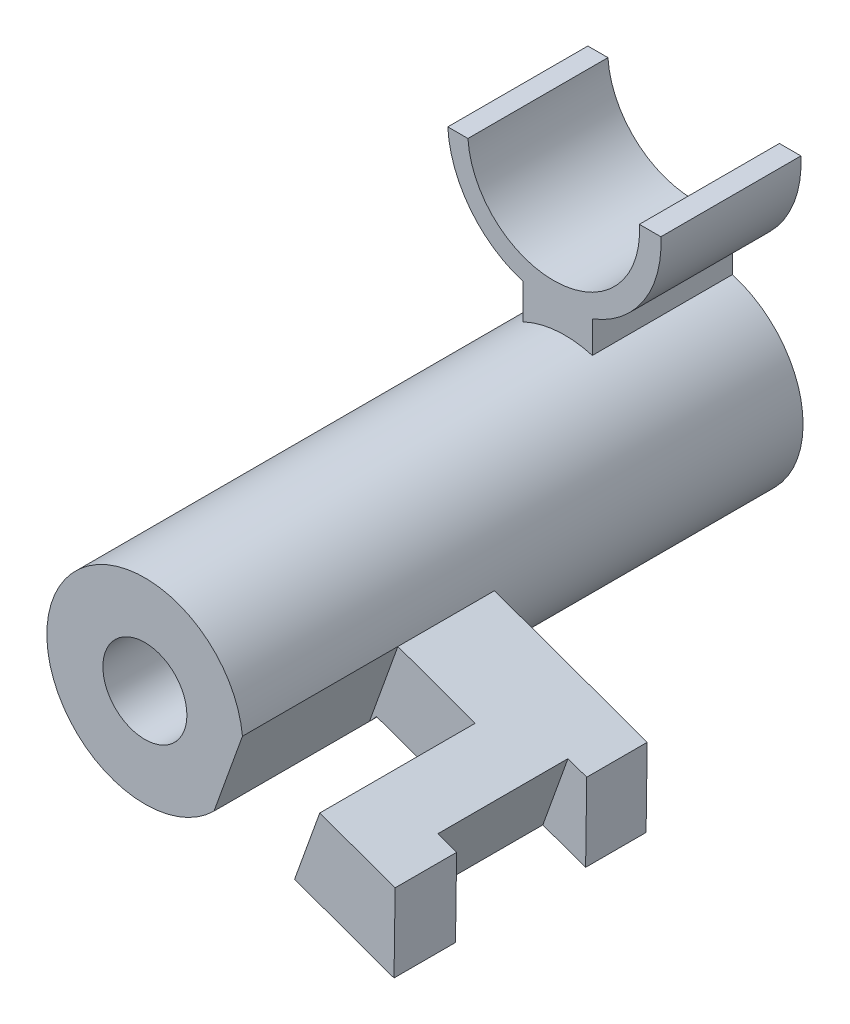
SolidWorks part; units mm, degrees
ref_plane "Front Plane" through (0, 0, 0) normal (0, 0, 1) x (1, 0, 0)
ref_plane "Top Plane" through (0, 0, 0) normal (0, 1, 0) x (1, 0, 0)
ref_plane "Right Plane" through (0, 0, 0) normal (1, 0, 0) x (0, 0, -1)
sketch "Sketch3" plane through (0, 0, 0) normal (0, 0, 1) x (1, 0, 0)
  circle A1 centre (-29.1148, 50.9477) radius 17.5
  dimension "D1" = 35
extrude "Boss-Extrude2" add sketch "Sketch3" against normal blind 100 separate body
sketch "Sketch4" plane through (0, 0, 0) normal (0, 0, 1) x (1, 0, 0)
  circle A0 centre (-29.1148, 50.9477) radius 7.5
  dimension "D1" = 15
extrude "Cut-Extrude2" cut sketch "Sketch4" against normal blind 100
ref_plane "Plane1" through (-12, 0, 0) normal (1, 0, 0) x (0, 0, -1)
sketch "Sketch16" plane through (0, 0, 0) normal (0, 0, 1) x (1, 0, 0)
  line L0 (-11.6981, 52.6534) -> (15.5591, 42.849)
  line L1 (-15.5292, 39.9167) -> (15.3598, 28.806)
  line L3 (15.5591, 42.849) -> (15.3598, 28.806)
  line L4 (-11.6981, 52.6534) -> (-15.5292, 39.9167)
  circle A0 centre (-29.1148, 50.9477) radius 7.5 construction
  circle A1 centre (-29.1148, 50.9477) radius 17.5 construction
  point P4 (-29.1148, 50.9477)
extrude "Boss-Extrude6" add sketch "Sketch16" against normal blind 45
sketch "Sketch18" plane through (15.4295, 42.8956, 0) normal (0.3385, 0.941, 0) x (0.941, -0.3385, 0)
  line L1 (-28.8292, 0) -> (-14.162, 0)
  line L2 (-28.8292, 0) -> (-28.8292, 27.7525)
  line L3 (-28.8292, 27.7525) -> (-14.162, 27.7525)
  line L4 (-14.162, 0) -> (-14.162, 27.7525)
extrude "Cut-Extrude6" cut sketch "Sketch18" against normal blind 45
sketch "Sketch19" plane through (15.4295, 42.8956, 0) normal (0.3385, 0.941, 0) x (0.941, -0.3385, 0)
  line L1 (-3.414, 10.9759) -> (12.5268, 10.9759)
  line L2 (-3.414, 10.9759) -> (-3.414, 34.2038)
  line L3 (-3.414, 34.2038) -> (12.5268, 34.2038)
  line L4 (12.5268, 10.9759) -> (12.5268, 34.2038)
extrude "Cut-Extrude8" cut sketch "Sketch19" against normal blind 45
sketch "Sketch20" plane through (0, 0, -100) normal (0, 0, -1) x (-1, 0, 0)
  line L0 (12, 34.8813) -> (12, -34.8813) construction
  line L1 (12, 92.2266) -> (15.8418, 92.2266)
  line L2 (46.4461, 90.1967) -> (50.0374, 90.1967)
  line L3 (24.2357, 73.4147) -> (24.2357, 67.7537)
  line L4 (36.5894, 72.9988) -> (36.5894, 66.7711)
  arc A0 (12, 92.2266) -> (50.0374, 90.1967) centre (31.0187, 91.2117) ccw
  arc A1 (15.8418, 92.2266) -> (46.4461, 90.1967) centre (31.144, 91.2117) ccw
  arc A2 (24.2357, 73.4147) -> (36.5894, 72.9988) centre (31.0187, 91.2117) ccw
  circle A3 centre (29.1148, 50.9477) radius 17.5 construction
  arc A4 (24.2357, 67.7537) -> (36.5894, 66.7711) centre (29.1148, 50.9477) cw
  circle M6 centre (29.1148, 50.9477) radius 17.5
extrude "Boss-Extrude8" add sketch "Sketch20" against normal blind 25 contours A1 L1 A0 L2 | A0 L3 L4 M6
